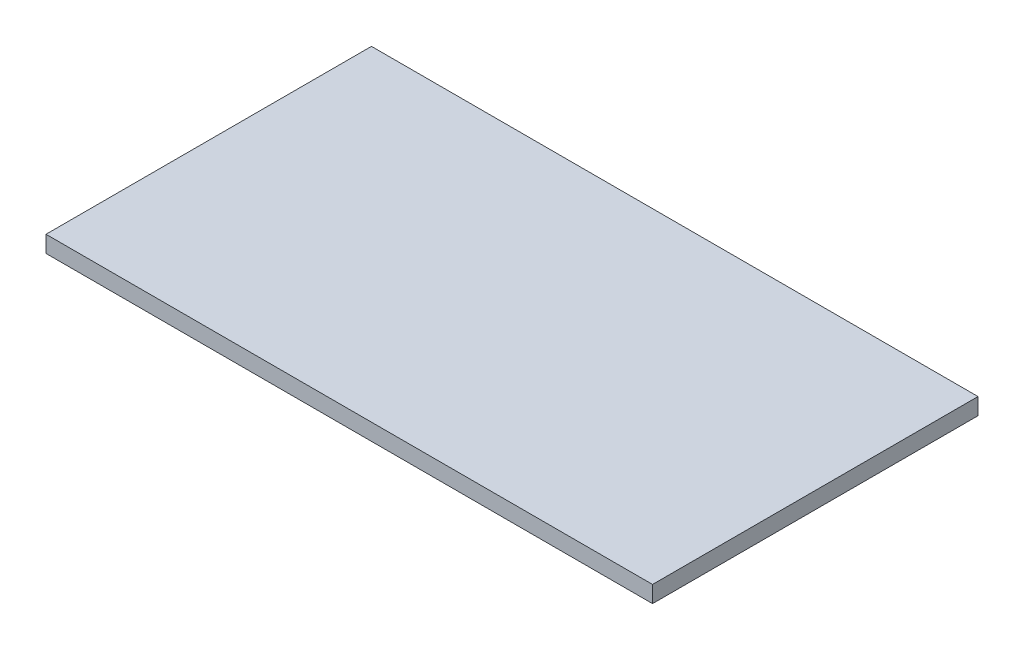
SolidWorks part; units mm, degrees
ref_plane "Front Plane" through (0, 0, 0) normal (0, 0, 1) x (1, 0, 0)
ref_plane "Top Plane" through (0, 0, 0) normal (0, 1, 0) x (1, 0, 0)
ref_plane "Right Plane" through (0, 0, 0) normal (1, 0, 0) x (0, 0, -1)
sketch "Sketch1" plane through (0, 0, 0) normal (0, 1, 0) x (1, 0, 0)
  line L1 (-206.6486, 106.0433) -> (314.0514, 106.0433)
  line L2 (-206.6486, 106.0433) -> (-206.6486, -173.3567)
  line L3 (-206.6486, -173.3567) -> (314.0514, -173.3567)
  line L4 (314.0514, 106.0433) -> (314.0514, -173.3567)
  dimension "D1" = 520.7
  dimension "D2" = 279.4
extrude "Boss-Extrude1" add sketch "Sketch1" along normal blind 14.2875
sketch "Sketch2" plane through (0, 0, 173.3567) normal (0, 0, 1) x (1, 0, 0)
  line L0 (53.7014, 0) -> (53.7014, 14.2875) construction
  line L1 (-206.6486, 0) -> (314.0514, 0) construction
  line L2 (-206.6486, 14.2875) -> (314.0514, 14.2875) construction
  line L3 (314.0514, 7.1437) -> (-206.6486, 7.1437) construction
  line L4 (314.0514, 14.2875) -> (314.0514, 0) construction
  line L5 (-206.6486, 14.2875) -> (-206.6486, 0) construction
sketch "Sketch3" plane through (0, 0, 0) normal (0, -1, 0) x (1, 0, 0)
  line L0 (53.7014, -106.0433) -> (53.7014, 173.3567) construction
  line L1 (314.0514, -106.0433) -> (-206.6486, -106.0433) construction
